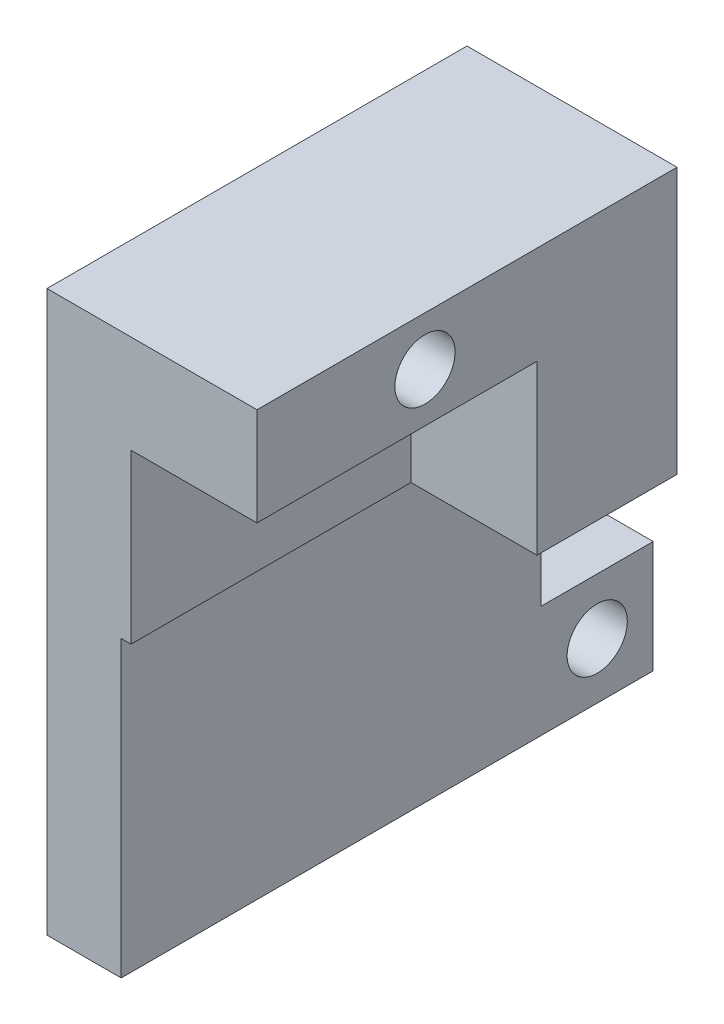
SolidWorks part; units mm, degrees
ref_plane "Front Plane" through (0, 0, 0) normal (0, 0, 1) x (1, 0, 0)
ref_plane "Top Plane" through (0, 0, 0) normal (0, 1, 0) x (1, 0, 0)
ref_plane "Right Plane" through (0, 0, 0) normal (1, 0, 0) x (0, 0, -1)
sketch "Sketch1" plane through (0, 0, 0) normal (0, 1, 0) x (1, 0, 0)
  line L1 (-12.5806, 31.4516) -> (-6.5806, 31.4516)
  line L2 (-12.5806, 31.4516) -> (-12.5806, -3.5484)
  line L3 (-12.5806, -3.5484) -> (-6.5806, -3.5484)
  line L4 (-6.5806, 31.4516) -> (-6.5806, -3.5484)
  dimension "D1" = 6
  dimension "D2" = 35
extrude "Boss-Extrude1" add sketch "Sketch1" along normal mid plane 40
sketch "Sketch2" plane through (-6.5806, 0, 0) normal (1, 0, 0) x (0, 0, -1)
  line L0 (31.4516, 20) -> (31.4516, -20) construction
  line L1 (-3.5484, 20) -> (31.4516, 20)
  line L2 (-3.5484, 20) -> (-3.5484, 13)
  line L3 (-3.5484, 13) -> (31.4516, 13)
  line L4 (31.4516, 20) -> (31.4516, 13)
  dimension "D1" = 7
extrude "Boss-Extrude2" add sketch "Sketch2" along normal blind 9
sketch "Sketch6" plane through (2.4194, 0, 0) normal (1, 0, 0) x (0, 0, -1)
  line L0 (-3.5484, 20) -> (-3.5484, 13) construction
  line L1 (31.4516, 20) -> (-3.5484, 20) construction
  circle A0 centre (13.4516, 16.5) radius 2 construction
  circle A1 centre (13.4516, 16.5) radius 2.15
  dimension "D1" = 0.15
  dimension "D2" = 17
  dimension "D3" = 3.5
extrude "Cut-Extrude1" cut sketch "Sketch6" against normal through all
sketch "Sketch7" plane through (0, 0, -31.4516) normal (0, 0, -1) x (-1, 0, 0)
  line L0 (6.5806, 13) -> (6.5806, -20) construction
  line L1 (6.5806, -12) -> (12.5806, -12)
  line L2 (6.5806, -12) -> (6.5806, -20)
  line L3 (6.5806, -20) -> (12.5806, -20)
  line L4 (12.5806, -12) -> (12.5806, -20)
  dimension "D1" = 8
extrude "Boss-Extrude3" add sketch "Sketch7" along normal blind 8
sketch "Sketch8" plane through (-12.5806, 0, 0) normal (-1, 0, 0) x (0, 0, 1)
  line L0 (-39.4516, -20) -> (-39.4516, -12) construction
  line L1 (-39.4516, -12) -> (-31.4516, -12) construction
  circle A0 centre (-35.4516, -16) radius 2 construction
  circle A1 centre (-35.4516, -16) radius 2.15
  dimension "D1" = 4
  dimension "D2" = 4
  dimension "D3" = 0.15
extrude "Cut-Extrude2" cut sketch "Sketch8" against normal through all
sketch "Sketch9" plane through (0, 13, 0) normal (0, -1, 0) x (1, 0, 0)
  line L0 (-6.5806, 3.5484) -> (-6.5806, -39.4516) construction
  line L1 (2.4194, -31.4516) -> (-6.5806, -31.4516)
  line L2 (2.4194, -31.4516) -> (2.4194, -21.4516)
  line L3 (2.4194, -21.4516) -> (-6.5806, -21.4516)
  line L4 (-6.5806, -31.4516) -> (-6.5806, -21.4516)
  dimension "D1" = 10
extrude "Boss-Extrude4" add sketch "Sketch9" along normal blind 12
sketch "Sketch10" plane through (-12.5806, 0, 0) normal (-1, 0, 0) x (0, 0, 1)
  line L0 (-39.4516, -20) -> (3.5484, -20) construction
  line L1 (3.5484, 20) -> (-1.4516, 20)
  line L2 (3.5484, 20) -> (3.5484, -20)
  line L3 (3.5484, -20) -> (-1.4516, -20)
  line L4 (-1.4516, 20) -> (-1.4516, -20)
  dimension "D1" = 5
extrude "Cut-Extrude3" cut sketch "Sketch10" against normal up to next
sketch "Sketch11" plane through (-6.5806, 0, 0) normal (1, 0, 0) x (0, 0, -1)
  line L1 (31.4516, 1) -> (1.4516, 1)
  line L2 (31.4516, 1) -> (31.4516, -20)
  line L3 (31.4516, -20) -> (1.4516, -20)
  line L4 (1.4516, 1) -> (1.4516, -20)
extrude "Cut-Extrude4" cut sketch "Sketch11" against normal blind 0.7
sketch "Sketch12" plane through (-6.5806, 0, 0) normal (1, 0, 0) x (0, 0, -1)
  line L1 (31.4516, -12) -> (39.4516, -12)
  line L2 (31.4516, -12) -> (31.4516, -20)
  line L3 (31.4516, -20) -> (39.4516, -20)
  line L4 (39.4516, -12) -> (39.4516, -20)
extrude "Cut-Extrude5" cut sketch "Sketch12" against normal blind 0.7
